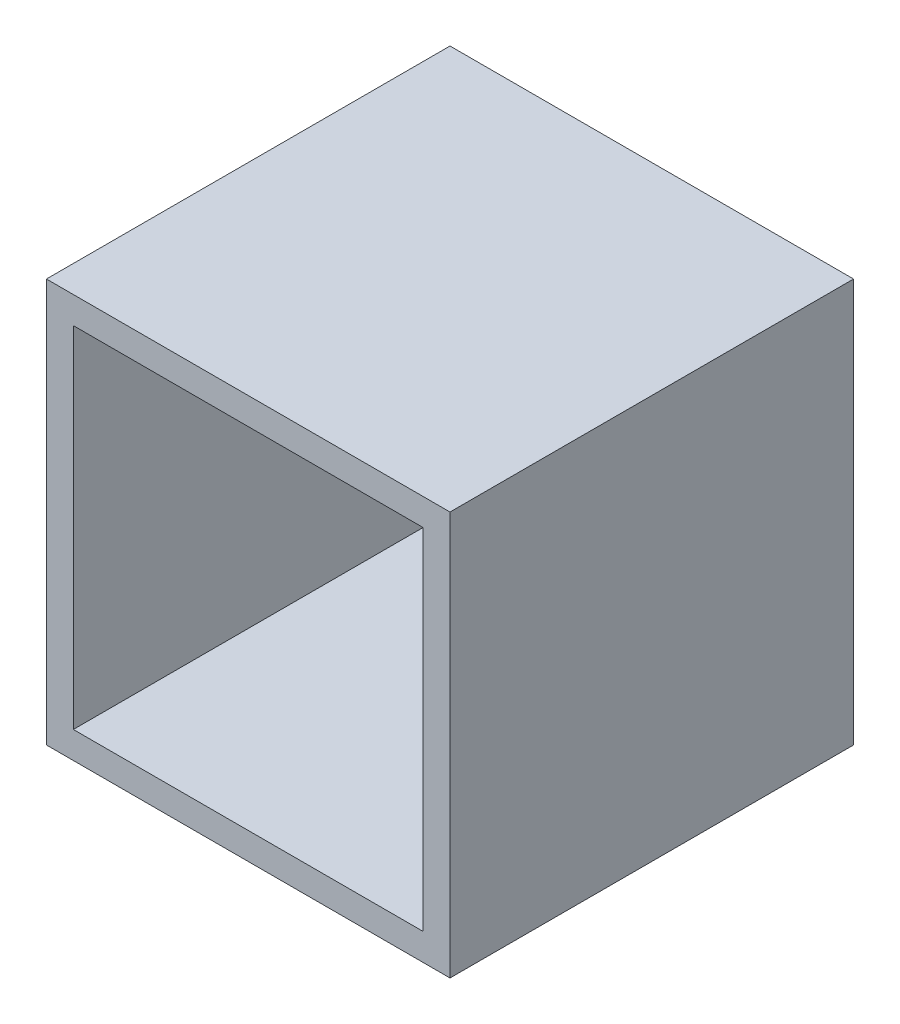
SolidWorks part; units mm, degrees
ref_plane "前视基准面" through (0, 0, 0) normal (0, 0, 1) x (1, 0, 0)
ref_plane "上视基准面" through (0, 0, 0) normal (0, 1, 0) x (1, 0, 0)
ref_plane "右视基准面" through (0, 0, 0) normal (1, 0, 0) x (0, 0, -1)
other "Configuration Table"
sketch "草图1" plane through (0, 0, 0) normal (0, 0, 1) x (1, 0, 0)
  line L1 (-4.6255, 27.5183) -> (25.3745, 27.5183)
  line L2 (-4.6255, 27.5183) -> (-4.6255, -2.4817)
  line L3 (-4.6255, -2.4817) -> (25.3745, -2.4817)
  line L4 (25.3745, 27.5183) -> (25.3745, -2.4817)
  dimension "D1" = 30
  dimension "D2" = 30
extrude "凸台-拉伸1" add sketch "草图1" along normal blind 30
sketch "草图2" plane through (0, 0, 30) normal (0, 0, 1) x (1, 0, 0)
  line L0 (-2.6255, 25.5183) -> (-2.6255, -0.4817)
  line L1 (-4.6255, 27.5183) -> (25.3745, 27.5183) construction
  line L2 (-4.6255, 27.5183) -> (-4.6255, -2.4817) construction
  line L3 (-4.6255, -2.4817) -> (25.3745, -2.4817) construction
  line L4 (25.3745, 27.5183) -> (25.3745, -2.4817) construction
  line L5 (-2.6255, -0.4817) -> (23.3745, -0.4817)
  line L6 (23.3745, 25.5183) -> (23.3745, -0.4817)
  line L7 (-2.6255, 25.5183) -> (23.3745, 25.5183)
  dimension "D1" = 2
extrude "切除-拉伸2" cut sketch "草图2" against normal blind 28 contours L7 L0 L5 L6 | L2 L1 L4 L3
